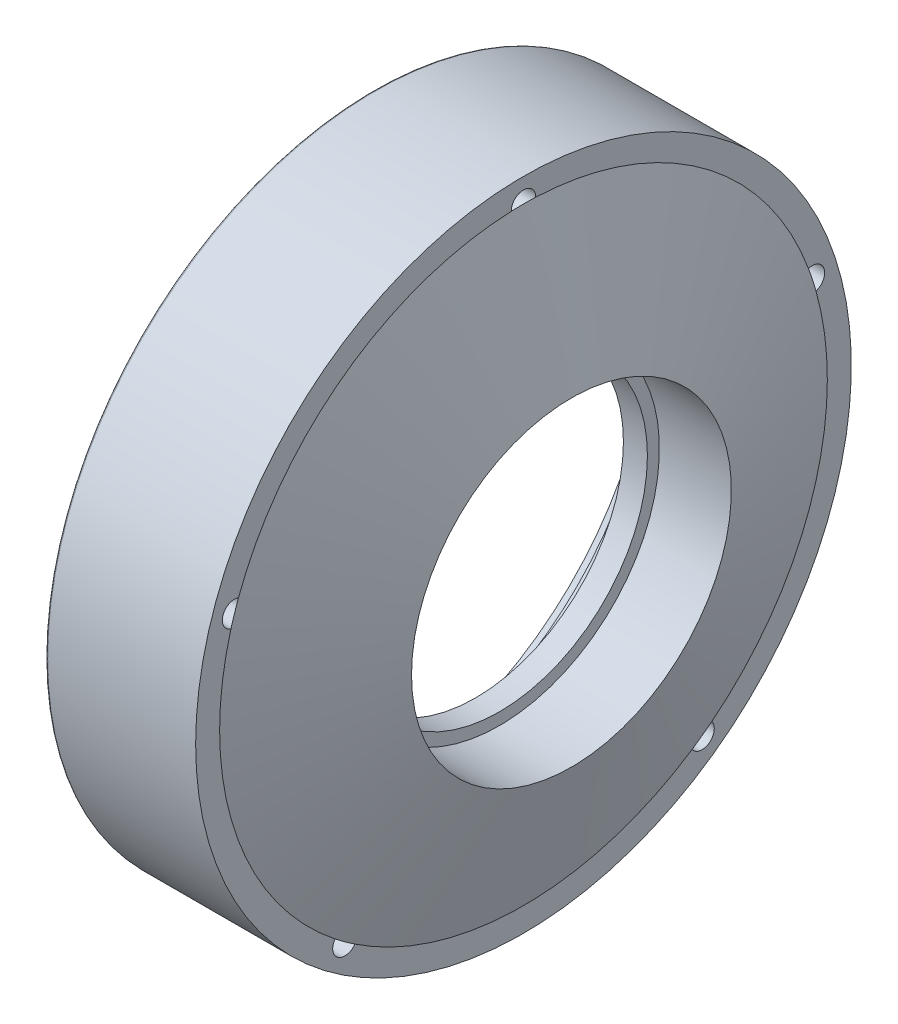
SolidWorks part; units mm, degrees
ref_plane "Front Plane" through (0, 0, 0) normal (0, 0, 1) x (1, 0, 0)
ref_plane "Top Plane" through (0, 0, 0) normal (0, 1, 0) x (1, 0, 0)
ref_plane "Right Plane" through (0, 0, 0) normal (1, 0, 0) x (0, 0, -1)
sketch "Sketch1" plane through (0, 0, 0) normal (0, 0, 1) x (1, 0, 0)
  line L0 (0, 152) -> (74.9977, 152) construction
  line L1 (74.9977, 164) -> (74.9977, 152)
  line L3 (0, 164) -> (74.9977, 164)
  line L5 (43, 130) -> (43, 108)
  line L8 (0, 0) -> (138.1049, 0) construction
  line L10 (62.9977, 80) -> (98.9909, 80)
  line L15 (43, 130) -> (10, 130)
  line L16 (10, 130) -> (10, 140)
  line L17 (10, 140) -> (0, 140)
  line L18 (0, 140) -> (0, 164)
  line L19 (62.9977, 80) -> (62.9977, 74)
  line L20 (62.9977, 74) -> (50.9977, 74)
  line L21 (50.9977, 74) -> (50.9977, 84)
  line L22 (50.9977, 84) -> (43, 108)
  line L23 (74.9977, 152) -> (98.9909, 80)
  point P1 (0, 152)
  point P3 (97.6725, 80)
  point P7 (0, 0)
  point P20 (0, 0)
  dimension "D1" = 130
  dimension "D2" = 22
  dimension "D3" = 10
  dimension "D4" = 80
  dimension "D5" = 24
  dimension "D6" = 10
  dimension "D8" = 12
  dimension "D9" = 10
  dimension "D10" = 74
revolve "Revolve1" add sketch "Sketch1" angle 360 about L8
sketch "Sketch2" plane through (74.9977, 0, 0) normal (1, 0, 0) x (0, 0, -1)
  circle A0 centre (0, 152) radius 6.1
  dimension "D1" = 12.2
extrude "Cut-Extrude1" cut sketch "Sketch2" against normal up to surface (74.9977 mm away) up to face at (0, 0, 164)
pattern_circular "CirPattern1" count 5 over 360 about axis through (0, 0, 0) along (1, 0, 0) of "Cut-Extrude1"
fillet "Fillet8" radius 1 1 edges at (0, 0, 164)
